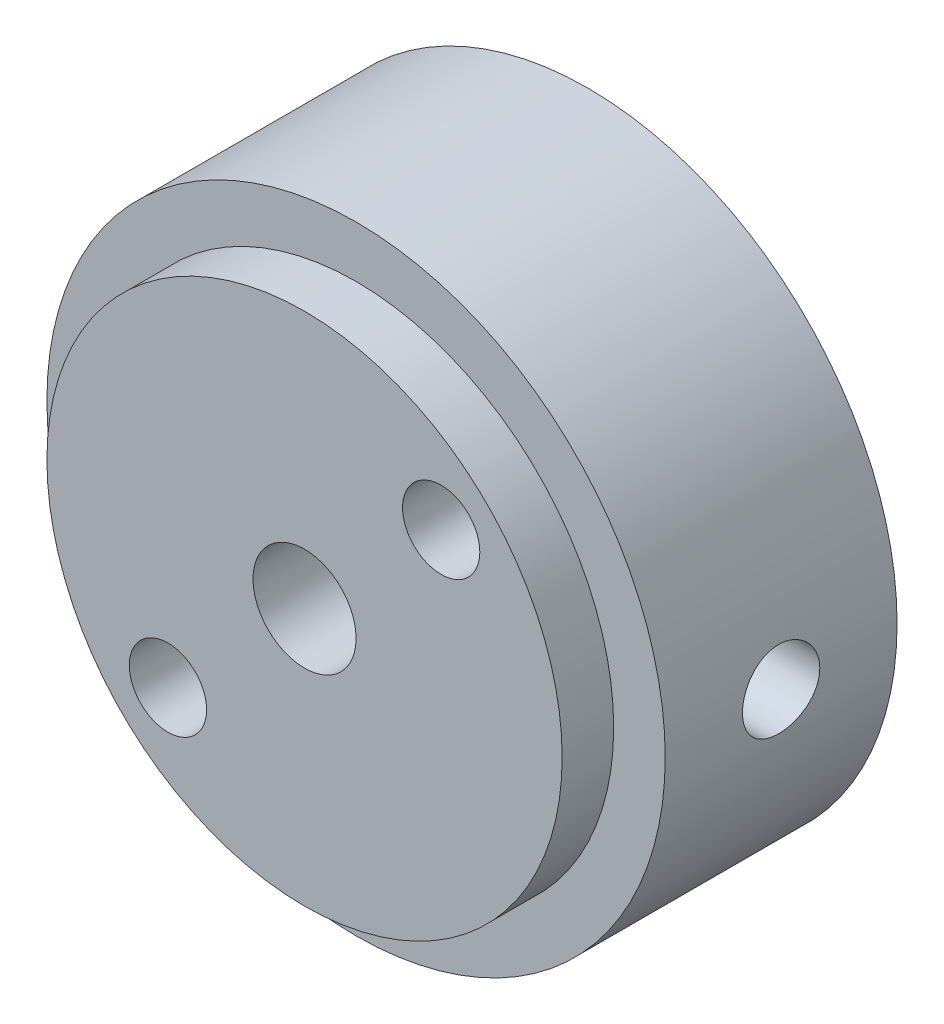
SolidWorks part; units mm, degrees
ref_plane "Front" through (0, 0, 0) normal (0, 0, 1) x (1, 0, 0)
ref_plane "Top" through (0, 0, 0) normal (0, 1, 0) x (1, 0, 0)
ref_plane "Right" through (0, 0, 0) normal (1, 0, 0) x (0, 0, -1)
sketch "Esquisse1" plane through (0, 0, 0) normal (0, 0, 1) x (1, 0, 0)
  circle A0 centre (0, 0) radius 12
  dimension "D1" = 24
extrude "Boss.-Extru.1" add sketch "Esquisse1" along normal blind 9
sketch "Esquisse2" plane through (0, 0, 9) normal (0, 0, 1) x (1, 0, 0)
  circle A0 centre (0, 0) radius 10
  dimension "D1" = 20
extrude "Boss.-Extru.2" add sketch "Esquisse2" along normal blind 2
sketch "Esquisse3" plane through (0, 0, 11) normal (0, 0, 1) x (1, 0, 0)
  line L0 (5.3033, 5.3033) -> (-5.3033, -5.3033) construction
  line L1 (0, 0) -> (-10, 0) construction
  circle A0 centre (-5.3033, -5.3033) radius 1.5
  circle A1 centre (5.3033, 5.3033) radius 1.5
  circle A2 centre (0, 0) radius 2
  circle A3 centre (0, 0) radius 10 construction
  point P5 (0, 0)
  dimension "D2" = 3
  dimension "D3" = 4
  dimension "D1" = 15
  dimension "D4" = 45
extrude "Enlèv. mat.-Extru.1" cut sketch "Esquisse3" against normal through all
sketch "Esquisse4" plane through (0, 0, 0) normal (0, 1, 0) x (1, 0, 0)
  line L0 (0, -4.5) -> (0, 0) construction
  circle A0 centre (0, -4.5) radius 1.5
  dimension "D1" = 3
  dimension "D2" = 4.5
extrude "Enlèv. mat.-Extru.2" cut sketch "Esquisse4" against normal through all
pattern_circular "Répétition circulaire1" count 2 over 90 about axis through (0, 0, 9) along (0, 0, 1) of "Enlèv. mat.-Extru.2"
